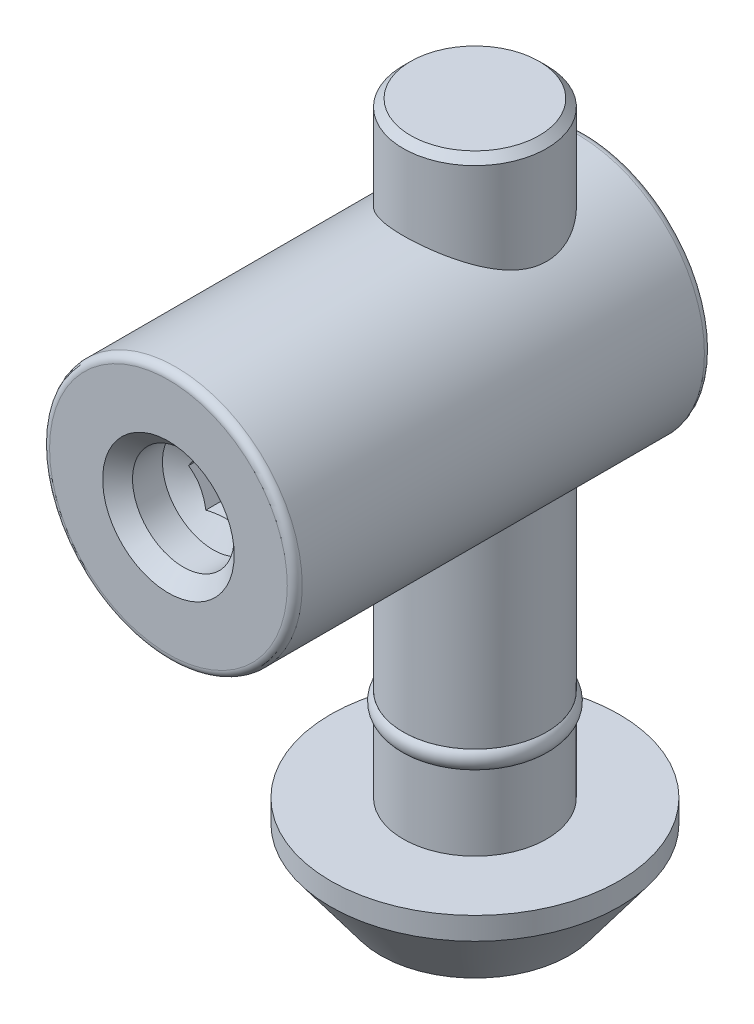
SolidWorks part; units mm, degrees
ref_plane "Спереди" through (0, 0, 0) normal (0, 0, 1) x (1, 0, 0)
ref_plane "Сверху" through (0, 0, 0) normal (0, 1, 0) x (1, 0, 0)
ref_plane "Справа" through (0, 0, 0) normal (1, 0, 0) x (0, 0, -1)
sketch "Эскиз3" plane through (0, 0, 0) normal (0, 0, 1) x (1, 0, 0)
  line L0 (0, 0) -> (-4.8, 0)
  line L1 (-4.8, 0) -> (-4.8, -34.3)
  line L2 (-4.8, -34.3) -> (-4.3, -34.3)
  line L3 (-4.3, -34.3) -> (-4.3, -35.5)
  line L4 (-4.3, -35.5) -> (-4.8, -35.5)
  line L5 (-4.8, -35.5) -> (-4.8, -40.5)
  line L7 (0, -46.5) -> (0, 0)
  line L8 (0, 0) -> (0, 5.384) construction
  line L9 (-4.8, -40.5) -> (-9.65, -40.5)
  line L10 (-9.65, -40.5) -> (-9.65, -42)
  line L11 (-9.65, -42) -> (-6.3, -46.5)
  line L12 (-6.3, -46.5) -> (0, -46.5)
  dimension "D1" = 9.6
  dimension "D2" = 1.2
  dimension "D3" = 46.5
  dimension "D4" = 0.5
  dimension "D5" = 5
  dimension "D6" = 6
  dimension "D7" = 1.5
  dimension "D8" = 1.5
  dimension "D9" = 19.3
revolve "Повернуть1" add sketch "Эскиз3" angle 360 about L8
chamfer "Фаска1" distance 0.5 angle 45 1 edges at (0, 0, -4.8)
sketch "Эскиз12" plane through (0, 0, 0) normal (0, 0, 1) x (1, 0, 0)
  line L0 (4.3, 0) -> (-4.3, 0) construction
  circle A0 centre (0, -14) radius 8.45
  dimension "D1" = 16.9
  dimension "D2" = 14
extrude "Бобышка-Вытянуть2" add sketch "Эскиз12" along normal blind 20.5 and the other way blind 7.4
hole_wizard "Отверстие обработанное метчиком M81" positions "Эскиз13" profile "Эскиз14" tap size "M8" standard "ISO"
sketch "Эскиз13" plane through (0, 0, 20.5) normal (0, 0, 1) x (1, 0, 0)
  point P0 (0, -14)
cosmetic thread "Отверстие резьбы1" parameters "D1"=3, "D2"=8
sketch "Эскиз14" plane through (0, -14, 20.5) normal (1, 0, 0) x (0, -1, 0)
  line L0 (0, 0) -> (0, 5.0429)
  line L1 (0, 5.0429) -> (3.4, 3)
  line L2 (3.4, 3) -> (3.4, 1)
  line L3 (3.4, 1) -> (4.4, 0)
  line L5 (4.4, 0) -> (0, 0)
  line L6 (-3.4, 1) -> (-4.4, 0) construction
  line L10 (0, 5.0429) -> (-3.4, 3) construction
  line L11 (0, -6.35) -> (0, 107.95) construction
  dimension "Диаметр сверла" = 6.8
  dimension "Глубина сверла" = 3
  dimension "Диаметр передней зенковки" = 8.8
  dimension "Угол передней зенковки" = 90
  dimension "Угол заточки сверла" = 118
fillet "Скругление1" radius 0.5 2 edges at (8.45, -14, -7.4) (8.45, -14, 20.5)
sketch "Эскиз15" plane through (0, 0, 20.5) normal (0, 0, 1) x (1, 0, 0)
  line L1 (2.3094, -14) -> (1.1547, -12)
  line L2 (1.1547, -12) -> (-1.1547, -12)
  line L3 (-1.1547, -12) -> (-2.3094, -14)
  line L4 (-2.3094, -14) -> (-1.1547, -16)
  line L5 (-1.1547, -16) -> (1.1547, -16)
  line L6 (1.1547, -16) -> (2.3094, -14)
  circle A0 centre (0, -14) radius 2 construction
  dimension "D1" = 4
extrude "Вырез-Вытянуть2" cut sketch "Эскиз15" against normal blind 6
sketch "Эскиз16" plane through (0, 0, 0) normal (0, 0, 1) x (1, 0, 0)
  line L0 (-4.3, -34.3) -> (-4.8, -34.3)
  line L1 (-4.3, -34.3) -> (-4.3, -35.5) construction
  line L2 (-4.8, -35.5) -> (-4.3, -35.5)
  line L3 (-4.3, -35.5) -> (-4.3, -34.3)
  line L4 (-4.3, -34.3) -> (4.3, -34.3) construction
  line L7 (-4.8, -20.9543) -> (-4.8, -34.3) construction
  line L8 (4.8, -35.5) -> (-4.8, -35.5) construction
  line L9 (0, -34.3) -> (0, -35.5) construction
  arc A0 (-4.8, -34.3) -> (-4.8, -35.5) centre (-4.3, -34.9) ccw
  point P15 (-4.3, -34.9)
revolve "Повернуть2" add sketch "Эскиз16" angle 360 about L9
